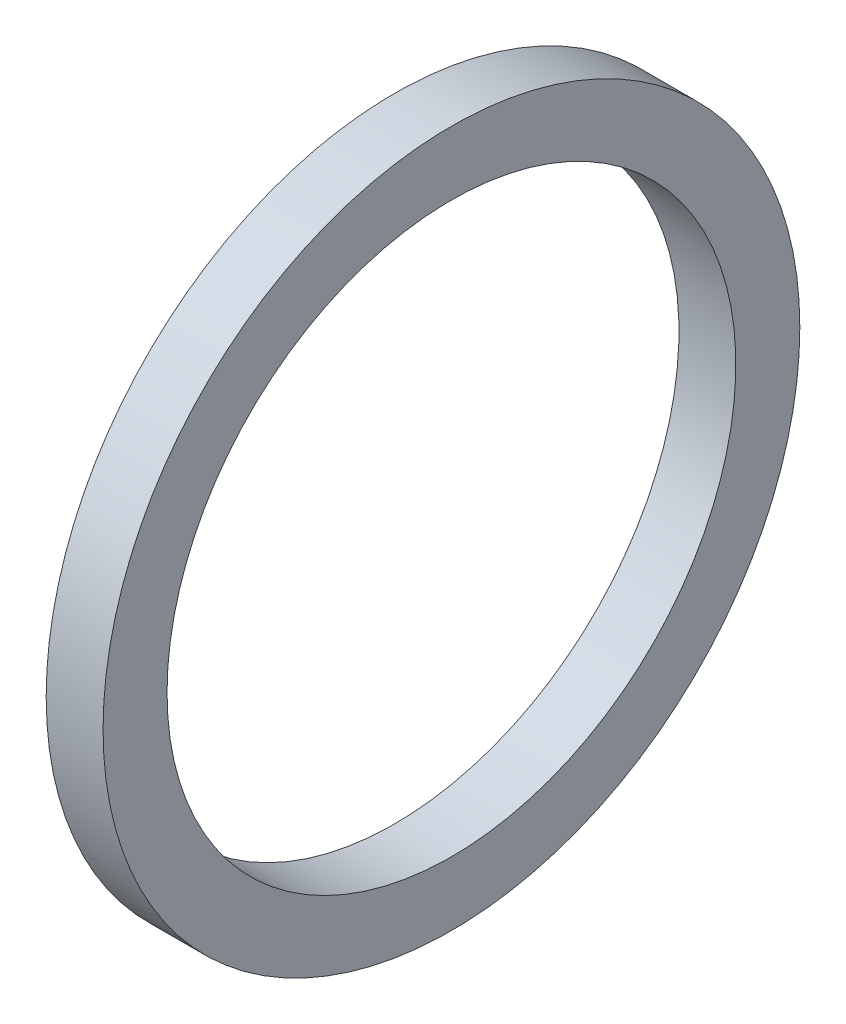
SolidWorks part; units mm, degrees
ref_plane "Front Plane" through (0, 0, 0) normal (0, 0, 1) x (1, 0, 0)
ref_plane "Top Plane" through (0, 0, 0) normal (0, 1, 0) x (1, 0, 0)
ref_plane "Right Plane" through (0, 0, 0) normal (1, 0, 0) x (0, 0, -1)
sketch "Sketch1" plane through (0, 0, 0) normal (0, 0, 1) x (1, 0, 0)
  line L0 (-43.7166, 0) -> (79.6876, 0) construction
  line L2 (0, -10.16) -> (2.032, -10.16)
  line L3 (0, -10.16) -> (0, -12.446)
  line L4 (0, -12.446) -> (2.032, -12.446)
  line L5 (2.032, -10.16) -> (2.032, -12.446)
  dimension "A" = 20.32
  dimension "B" = 24.892
  dimension "C" = 2.032
revolve "Revolve1" add sketch "Sketch1" angle 360 about L0
sketch "Sketch2" [suppressed] plane through (0, 0, 0) normal (0, 0, 1) x (1, 0, 0)
  line L0 (-34.685, 0) -> (47.6686, 0) construction
  circle A0 centre (2.54, -5.715) radius 0.762
  dimension "D1" = 2.54
  dimension "E" = 1.778
  dimension "D" = 17.018
revolve "Revolve3" [suppressed] add sketch "Sketch2" angle 360 about L0
